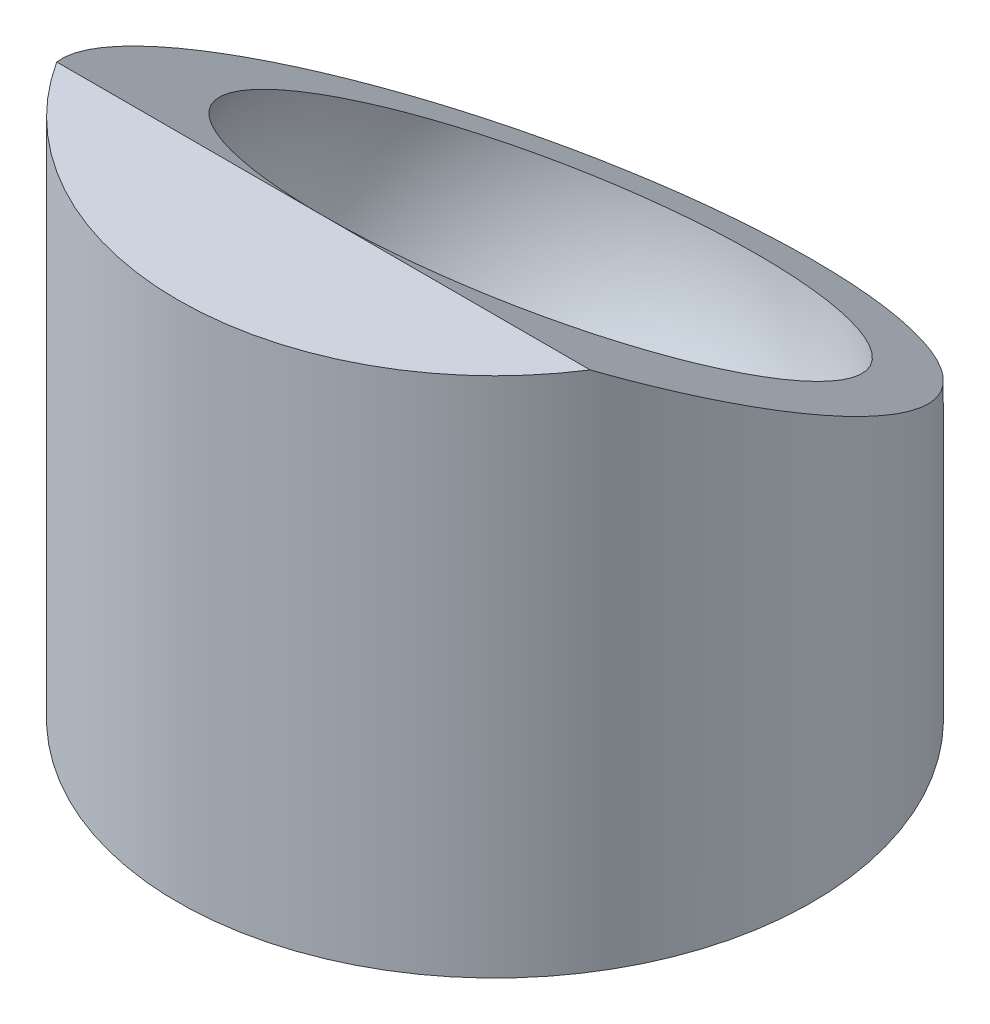
SolidWorks part; units mm, degrees
ref_plane "Front Plane" through (0, 0, 0) normal (0, 0, 1) x (1, 0, 0)
ref_plane "Top Plane" through (0, 0, 0) normal (0, 1, 0) x (1, 0, 0)
ref_plane "Right Plane" through (0, 0, 0) normal (1, 0, 0) x (0, 0, -1)
sketch "Sketch1" plane through (0, 0, 0) normal (1, 0, 0) x (0, 0, -1)
  line L0 (-5.05, 8.7469) -> (0, 0) construction
  line L1 (0, 0) -> (-10.1, 0) construction
  line L2 (-5.05, 8.7469) -> (-12, 8.7469)
  line L3 (-12, 8.7469) -> (-12, -12)
  line L4 (-12, -12) -> (0, -12)
  line L7 (0, -12) -> (0, -10.1)
  arc A0 (0, -10.1) -> (-5.05, 8.7469) centre (0, 0) cw
  dimension "D1" = 10.1
  dimension "D4" = 12
  dimension "D2" = 60
  dimension "D3" = 12
revolve "Revolve1" add sketch "Sketch1" angle 360 about L7
sketch "Sketch2" plane through (0, 0, 0) normal (1, 0, 0) x (0, 0, -1)
  line L0 (0, 0) -> (-8.7469, 5.05) construction
  line L1 (0, 0) -> (-10.1, 0) construction
  line L2 (-6.4922, 7.737) -> (9.9466, -1.7538)
  line L7 (0, 0) -> (-6.4922, 7.737) construction
  line L8 (-12, 8.7469) -> (-12, -12) construction
  line L9 (-6.4922, 7.737) -> (-12, 7.737)
  line L11 (9.9466, -1.7538) -> (12, -2.9394)
  line L12 (12, -12) -> (12, 8.7469) construction
  line L13 (12, -2.9394) -> (12, 8.7469)
  line L14 (-12, 8.7469) -> (-12, -12) construction
  line L15 (-12, 7.737) -> (-12, 8.7469)
  line L16 (-12, 8.7469) -> (12, 8.7469)
  arc A0 (-5.05, 8.7469) -> (0, -10.1) centre (0, 0) ccw construction
  arc A1 (-5.05, 8.7469) -> (5.05, 8.7469) centre (0, 0) ccw construction
  dimension "D1" = 30
  dimension "D2" = 40
extrude "Cut-Extrude1" cut sketch "Sketch2" against normal through all both and the other way through all
